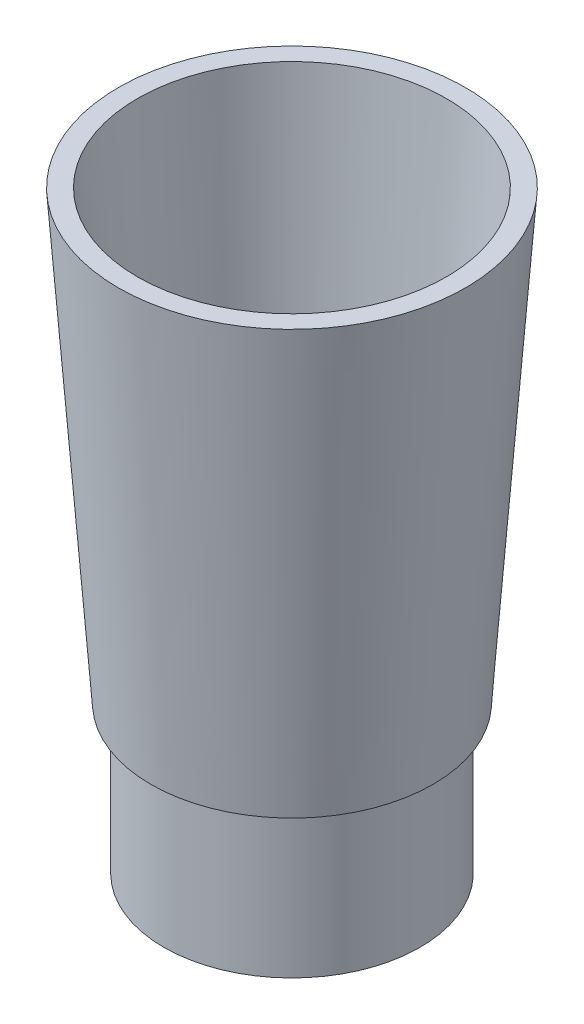
SolidWorks part; units mm, degrees
ref_plane "Front Plane" through (0, 0, 0) normal (0, 0, 1) x (1, 0, 0)
ref_plane "Top Plane" through (0, 0, 0) normal (0, 1, 0) x (1, 0, 0)
ref_plane "Right Plane" through (0, 0, 0) normal (1, 0, 0) x (0, 0, -1)
sketch "Sketch1" plane through (0, 0, 0) normal (0, 0, 1) x (1, 0, 0)
  line L0 (11.5, 0) -> (11.5, 17.5446)
  line L1 (55, 0) -> (-55, 0) construction
  line L2 (11.5, 17.5446) -> (13, 17.5446)
  line L3 (13, 17.5446) -> (16.273, 62.5446)
  line L4 (16.273, 62.5446) -> (18.2783, 62.5446)
  line L5 (18.2783, 62.5446) -> (14.8598, 15.5446)
  line L6 (14.8598, 15.5446) -> (13.5, 15.5446)
  line L7 (13.5, 15.5446) -> (13.5, 0)
  line L8 (13.5, 0) -> (11.5, 0)
  line L9 (0, -55) -> (0, 55) construction
  line L10 (0, 70.0735) -> (0, -30.6209) construction
  dimension "D1" = 11.5
  dimension "D2" = 2
  dimension "D3" = 2
  dimension "D4" = 2
  dimension "D5" = 94.16
  dimension "D6" = 13
  dimension "D7" = 45
revolve "Revolve1" add sketch "Sketch1" angle 360 about L10
